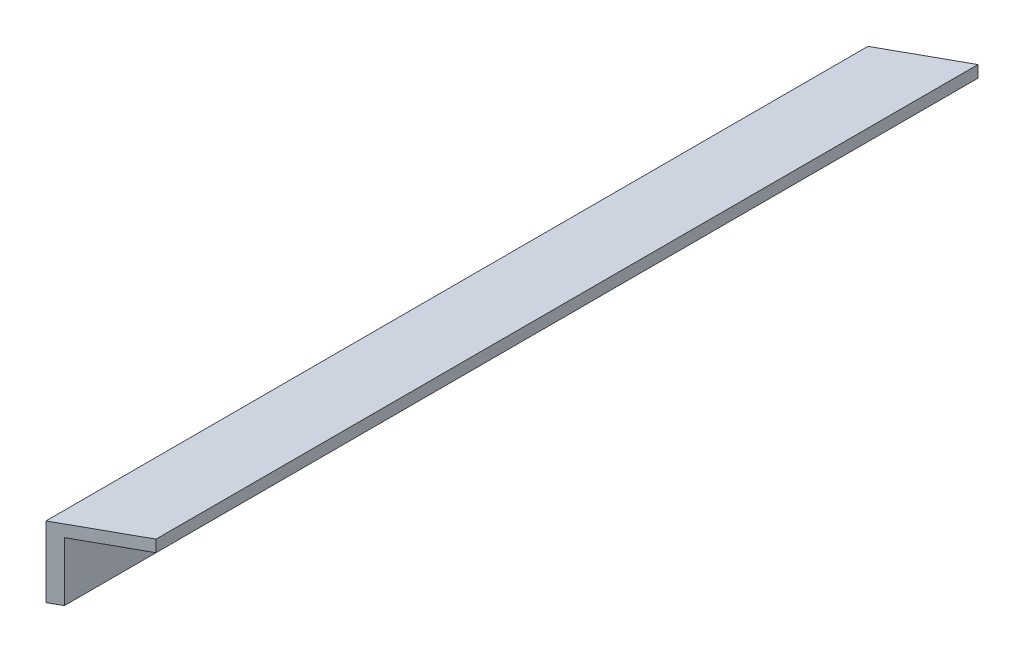
SolidWorks part; units mm, degrees
ref_plane "Front Plane" through (0, 0, 0) normal (0, 0, 1) x (1, 0, 0)
ref_plane "Top Plane" through (0, 0, 0) normal (0, 1, 0) x (1, 0, 0)
ref_plane "Right Plane" through (0, 0, 0) normal (1, 0, 0) x (0, 0, -1)
sketch "Sketch1" plane through (0, 0, 0) normal (0, 0, 1) x (1, 0, 0)
  line L0 (0, 0) -> (0, -38.1)
  line L1 (0, -38.1) -> (6.35, -38.1)
  line L2 (6.35, -38.1) -> (6.35, -6.35)
  line L3 (6.35, -6.35) -> (38.1, -6.35)
  line L4 (38.1, -6.35) -> (38.1, 0)
  line L5 (38.1, 0) -> (0, 0)
  dimension "D1" = 38.1
  dimension "D2" = 6.35
extrude "OAL Angle" add sketch "Sketch1" along normal blind 463.55
sketch "Sketch2" plane through (0, 0, 0) normal (0, 1, 0) x (1, 0, 0)
  line L1 (38.1, -463.55) -> (38.1, 0) construction
  line L5 (0, -463.55) -> (0, 0) construction
  line L8 (0, -231.775) -> (38.1, -231.775) construction
  line L9 (0, 0) -> (38.1, 0)
  line L10 (0, -21.1192) -> (0, 0)
  line L11 (38.1, 0) -> (0, -21.1192)
  line L12 (38.1, -463.55) -> (0, -463.55)
  line L13 (38.1, -442.4308) -> (38.1, -463.55)
  line L14 (0, -463.55) -> (38.1, -442.4308)
extrude "Angle Cutourt" cut sketch "Sketch2" against normal through all
